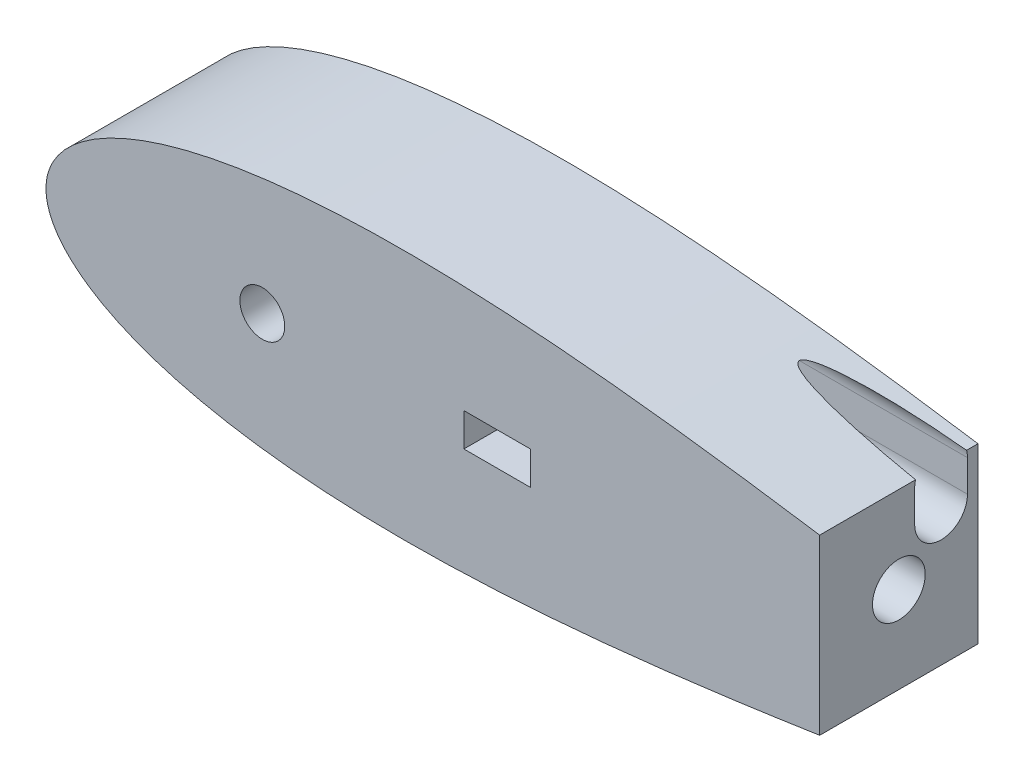
SolidWorks part; units mm, degrees
ref_plane "Front Plane" through (0, 0, 0) normal (0, 0, 1) x (1, 0, 0)
ref_plane "Top Plane" through (0, 0, 0) normal (0, 1, 0) x (1, 0, 0)
ref_plane "Right Plane" through (0, 0, 0) normal (1, 0, 0) x (0, 0, -1)
sketch "Sketch1" plane through (0, 0, 0) normal (0, 0, 1) x (1, 0, 0)
  line L0 (100, 0) -> (0, 0) construction
  line L1 (1.2169, -991.9959) -> (1.2169, 49008.0041) construction
  line L2 (93.345, 0) -> (114.935, 0) construction
  line L3 (125.634, 0) -> (131.6629, 0) construction
  line L4 (643.5991, 0) -> (643.5991, -1.016)
  line L9 (0, 0) -> (643.9668, 0)
  line L13 (460.661, 0) -> (473.361, 0)
  circle A0 centre (104.14, 0) radius 10.795 construction
  arc A1 (1.2169, -4.6585) -> (1.2169, 4.6585) centre (9.525, 0) cw
  arc A2 (641.5671, 0) -> (644.1071, 0) centre (642.8371, 0) ccw
  circle A4 centre (104.14, 0) radius 10.795
  circle A9 centre (40.64, 0) radius 12.7
  circle A14 centre (642.3793, 0) radius 1.5875 construction
  arc A15 (642.5108, -1.582) -> (642.5108, 1.582) centre (642.3793, 0) ccw
  spline S2 degree 3 poles (666.3448, -0.0547) (672.2538, 0) (666.3448, 0.0547) (662.8509, 0.2344) (656.505, 0.5436) (649.293, 1.0348) (640.4916, 1.7319) (630.4138, 2.6634) (619.0141, 3.8493) (606.375, 5.3044) (592.5439, 7.0376) (577.5855, 9.0506) (561.5643, 11.3389) (544.5497, 13.8907) (526.6141, 16.6877) (507.8326, 19.7051) (488.2827, 22.9117) (468.0444, 26.2704) (447.1994, 29.739) (425.8316, 33.2703) (404.0263, 36.8132) (381.8707, 40.3133) (359.4533, 43.7135) (336.8645, 46.9554) (314.1962, 49.9798) (291.5418, 52.7277) (268.9963, 55.1412) (246.6566, 57.1646) (224.6209, 58.7452) (202.9892, 59.8341) (181.8631, 60.3875) (161.3458, 60.367) (141.542, 59.7399) (122.5581, 58.4818) (104.5023, 56.5743) (87.485, 54.0089) (71.6197, 50.7848) (57.0237, 46.9125) (43.8205, 42.415) (32.1416, 37.3322) (22.1291, 31.7315) (13.9324, 25.7264) (7.6896, 19.5132) (3.4631, 13.4204) (1.1063, 7.9234) (0.1546, 3.5138) (-0.0622, 0) (0.1546, -3.5138) (1.1063, -7.9234) (3.4631, -13.4204) (7.6896, -19.5132) (13.9324, -25.7264) (22.1291, -31.7315) (32.1416, -37.3322) (43.8205, -42.415) (57.0237, -46.9125) (71.6197, -50.7848) (87.485, -54.0089) (104.5023, -56.5743) (122.5581, -58.4818) (141.542, -59.7399) (161.3458, -60.367) (181.8631, -60.3875) (202.9892, -59.8341) (224.6209, -58.7452) (246.6566, -57.1646) (268.9963, -55.1412) (291.5418, -52.7277) (314.1962, -49.9798) (336.8645, -46.9554) (359.4533, -43.7135) (381.8707, -40.3133) (404.0263, -36.8132) (425.8316, -33.2703) (447.1994, -29.739) (468.0444, -26.2704) (488.2827, -22.9117) (507.8326, -19.7051) (526.6141, -16.6877) (544.5497, -13.8907) (561.5643, -11.3389) (577.5855, -9.0506) (592.5439, -7.0376) (606.375, -5.3044) (619.0141, -3.8493) (630.4138, -2.6634) (640.4916, -1.7319) (649.293, -1.0348) (656.505, -0.5436) (662.8509, -0.2344) (666.3448, -0.0547) (672.2538, 0) (666.3448, 0.0547) knots -0.009667 -0.005395 -0.002168 0 0.002168 0.005395 0.009667 0.014967 0.021271 0.028553 0.036781 0.04592 0.055932 0.066773 0.078397 0.090755 0.103793 0.117456 0.131686 0.146422 0.1616 0.177156 0.193024 0.209135 0.225421 0.241812 0.258238 0.274629 0.290914 0.307025 0.322893 0.338448 0.353626 0.368361 0.38259 0.396253 0.40929 0.421647 0.43327 0.444109 0.454119 0.463255 0.471479 0.478755 0.485052 0.490344 0.49461 0.497833 0.5 0.502167 0.50539 0.509656 0.514948 0.521245 0.528521 0.536745 0.545881 0.555891 0.56673 0.578353 0.59071 0.603747 0.61741 0.631639 0.646374 0.661552 0.677107 0.692975 0.709086 0.725371 0.741762 0.758188 0.774579 0.790865 0.806976 0.822844 0.8384 0.853578 0.868314 0.882544 0.896207 0.909245 0.921603 0.933227 0.944068 0.95408 0.963219 0.971447 0.978729 0.985033 0.990333 0.994605 0.997832 1 1.002168 1.005395 1.009667 only from (670.56, 0) to (670.56, 0)
  point P2 (167.64, 0)
  point P8 (1.2169, -4.6585)
  point P10 (1.2169, 4.6585)
  point P28 (133.9182, 0)
  point P49 (130.0977, 0)
  point P59 (95.1064, 0)
  dimension "D2" = 21.59
  dimension "D3" = 1.016
  dimension "D4" = 1.27
  dimension "D8" = 25.4
  dimension "D9" = 63.5
  dimension "D10" = 3.175
  dimension "D6" = 63.5
extrude "Boss-Extrude1" add sketch "Sketch1" along normal blind 76.2 contours S2
sketch "Sketch3" plane through (0, 0, 76.2) normal (0, 0, 1) x (1, 0, 0)
  circle A0 centre (104.1392, 0) radius 10.795
  dimension "D1" = 21.59
extrude "Cut-Extrude2" cut sketch "Sketch3" against normal blind 76.2
sketch "Sketch4" plane through (0, 0, 76.2) normal (0, 0, 1) x (1, 0, 0)
sketch "Sketch6" plane through (0, 0, 0) normal (1, 0, 0) x (0, 0, -1)
  circle A0 centre (-20.32, 0) radius 6.35
  dimension "D1" = 12.7
  dimension "D2" = 20.32
extrude "Cut-Extrude3" cut sketch "Sketch6" against normal blind 0.0003 and the other way blind 53.34
sketch "Sketch7" plane through (0, 0, 0) normal (0, 0, -1) x (-1, 0, 0)
  circle A0 centre (-38.1, 0) radius 1.5875
  circle A1 centre (-50.8, 0) radius 1.5875
  dimension "D1" = 3.175
  dimension "D2" = 3.175
  dimension "D3" = 12.7
  dimension "D4" = 38.1
extrude "Cut-Extrude4" cut sketch "Sketch7" against normal blind 30.48
sketch "Sketch8" plane through (0, 0, 0) normal (0, 0, -1) x (-1, 0, 0)
  line L1 (-677.2433, 63.9901) -> (-372.4433, 63.9901)
  line L2 (-677.2433, 63.9901) -> (-677.2433, -63.0099)
  line L3 (-677.2433, -63.0099) -> (-372.4433, -63.0099)
  line L4 (-372.4433, 63.9901) -> (-372.4433, -63.0099)
  dimension "D1" = 127
  dimension "D2" = 372.4433
  dimension "D3" = 304.8
extrude "Cut-Extrude5" cut sketch "Sketch8" against normal blind 76.2
sketch "Sketch9" plane through (372.4433, 0, 0) normal (1, 0, 0) x (0, 0, -1)
  line L0 (0, -41.7363) -> (0, 41.7363) construction
  circle A0 centre (-38.1, 0) radius 12.7
  dimension "D1" = 25.4
  dimension "D2" = 38.1
extrude "Cut-Extrude6" cut sketch "Sketch9" against normal blind 101.6 contours A0
sketch "Sketch10" plane through (0, 0, 0) normal (0, 0, -1) x (-1, 0, 0)
  line L0 (-372.4433, -41.7363) -> (-372.4433, 41.7363) construction
  circle A0 centre (-343.8683, 0) radius 3.175
  circle A1 centre (-286.7183, 0) radius 3.175
  dimension "D1" = 57.15
  dimension "D2" = 28.575
  dimension "D3" = 6.35
  dimension "D4" = 6.35
extrude "Cut-Extrude7" cut sketch "Sketch10" against normal blind 57.15
sketch "Sketch11" plane through (0, 0, 0) normal (0, 0, -1) x (-1, 0, 0)
  circle A0 centre (-286.7183, 0) radius 5.08
  circle A1 centre (-343.8683, 0) radius 5.08
  dimension "D1" = 10.16
extrude "Cut-Extrude8" cut sketch "Sketch11" against normal blind 6.35
sketch "Sketch12" plane through (0, 0, 0) normal (0, 0, -1) x (-1, 0, 0)
  circle A0 centre (-38.1, 0) radius 3.175
  circle A1 centre (-50.8, 0) radius 3.175
  dimension "D1" = 6.35
  dimension "D2" = 6.35
extrude "Cut-Extrude9" cut sketch "Sketch12" against normal blind 6.35
sketch "Sketch13" plane through (372.4433, 0, 0) normal (1, 0, 0) x (0, 0, -1)
  line L0 (-17.78, 23.2323) -> (-17.78, 38.4723) construction
  line L1 (-30.48, 23.2323) -> (-30.48, 38.4723)
  line L2 (-5.08, 23.2323) -> (-5.08, 38.4723)
  line L3 (0, -41.7363) -> (0, 41.7363) construction
  line L4 (-76.2, -41.7363) -> (-76.2, 41.7363) construction
  arc A0 (-30.48, 23.2323) -> (-5.08, 23.2323) centre (-17.78, 23.2323) ccw
  arc A1 (-5.08, 38.4723) -> (-30.48, 38.4723) centre (-17.78, 38.4723) ccw
  point P2 (-17.78, 30.8523)
  dimension "D1" = 5.08
  dimension "D2" = 45.72
  dimension "D4" = 15.24
extrude "Cut-Extrude10" cut sketch "Sketch13" against normal blind 198.458
sketch "Sketch15" plane through (0, 0, 0) normal (0, 0, -1) x (-1, 0, 0)
  line L0 (-372.4433, -41.7363) -> (-372.4433, 41.7363) construction
  line L1 (-261.3613, -30.48) -> (-173.9853, -30.48)
  line L2 (-261.3613, -30.48) -> (-261.3613, 30.48)
  line L3 (-261.3613, 30.48) -> (-173.9853, 30.48)
  line L4 (-173.9853, -30.48) -> (-173.9853, 30.48)
  point P4 (0, 0)
  point P5 (0, 0)
  point P6 (0, 0)
  point P7 (0, 0)
  dimension "D1" = 87.376
  dimension "D2" = 60.96
  dimension "D3" = 111.082
extrude "Cut-Extrude11" cut sketch "Sketch15" against normal blind 33.3
sketch "Sketch17" plane through (0, 0, 33.3) normal (0, 0, -1) x (-1, 0, 0)
  line L0 (-173.9853, -30.48) -> (-173.9853, 30.48) construction
  line L1 (-233.1711, 8) -> (-201.1711, 8)
  line L2 (-233.1711, 8) -> (-233.1711, -8)
  line L3 (-233.1711, -8) -> (-201.1711, -8)
  line L4 (-201.1711, 8) -> (-201.1711, -8)
  line L5 (-173.9853, 30.48) -> (-261.3613, 30.48) construction
  dimension "D1" = 27.1858
  dimension "D2" = 32
  dimension "D3" = 16
  dimension "D4" = 22.48
extrude "Cut-Extrude12" cut sketch "Sketch17" against normal blind 50.8
sketch "Sketch18" plane through (0, 0, 33.3) normal (0, 0, -1) x (-1, 0, 0)
  line L0 (-233.1711, 8) -> (-233.1711, -8) construction
  line L1 (-201.1711, -8) -> (-201.1711, 8) construction
  circle A0 centre (-199.4711, 0) radius 1.5
  circle A1 centre (-234.8711, 0) radius 1.5
  point P6 (-233.1711, 0)
  point P7 (0, 0)
  dimension "D1" = 3
  dimension "D2" = 3
  dimension "D3" = 1.7
  dimension "D4" = 1.7
extrude "Cut-Extrude13" cut sketch "Sketch18" against normal blind 25.4
sketch "Sketch19" plane through (0, 0, 0) normal (0, 0, -1) x (-1, 0, 0)
  line L1 (-166.0439, 28.3517) -> (-112.7039, 28.3517)
  line L2 (-166.0439, 28.3517) -> (-166.0439, 49.9417)
  line L3 (-166.0439, 49.9417) -> (-112.7039, 49.9417)
  line L4 (-112.7039, 28.3517) -> (-112.7039, 49.9417)
  dimension "D1" = 53.34
  dimension "D2" = 21.59
extrude "Cut-Extrude14" cut sketch "Sketch19" against normal blind 66.04
